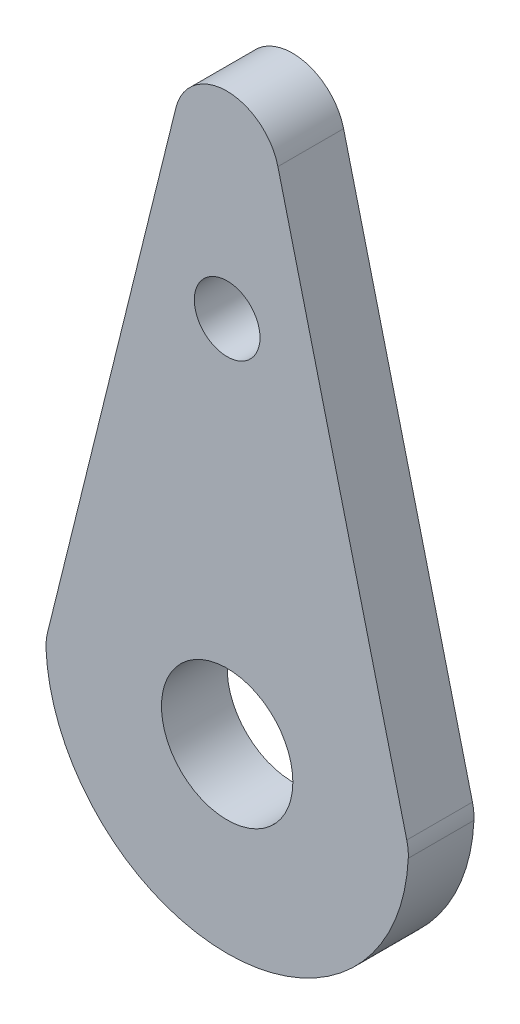
SolidWorks part; units mm, degrees
ref_plane "Front Plane" through (0, 0, 0) normal (0, 0, 1) x (1, 0, 0)
ref_plane "Top Plane" through (0, 0, 0) normal (0, 1, 0) x (1, 0, 0)
ref_plane "Right Plane" through (0, 0, 0) normal (1, 0, 0) x (0, 0, -1)
sketch "Sketch1" plane through (0, 0, 0) normal (0, 0, 1) x (1, 0, 0)
  line L0 (-8.6822, 0.3266) -> (-2.4777, 25.4)
  line L1 (2.453, 25.4022) -> (8.6816, 0.3278)
  circle A0 centre (0, 0) radius 3.175
  arc A1 (-8.7539, -0.3992) -> (8.7538, -0.4007) centre (0, 0) ccw
  arc A2 (2.453, 25.4022) -> (-2.4777, 25.4) centre (-0.0121, 24.7899) ccw
  circle A3 centre (0, 0) radius 8.763 construction
  arc A4 (-8.7539, -0.3992) -> (-8.6822, 0.3266) centre (-6.2165, -0.2835) cw
  arc A5 (8.7538, -0.4007) -> (8.6816, 0.3278) centre (6.2165, -0.2845) ccw
  point P12 (-8.763, 0)
  point P15 (8.763, 0)
  dimension "D1" = 6.35
  dimension "D3" = 2.54
  dimension "D6" = 2.54
  dimension "D7" = 2.54
  dimension "D4" = 25.4
  dimension "D5" = 25.4022
  dimension "D2" = 5.588
extrude "Boss-Extrude1" add sketch "Sketch1" along normal blind 3.175
hole_wizard "1/8 (0.125) Diameter Hole1" positions "Sketch3" profile "Sketch2" hole size "1/8" standard "ANSI Inch"
sketch "Sketch3" plane through (0, 0, 3.175) normal (0, 0, 1) x (1, 0, 0)
  arc A0 (2.453, 25.4022) -> (-2.4777, 25.4) centre (-0.0121, 24.7899) ccw construction
  point P0 (0, 17.8049)
  point P3 (-0.0132, 27.3299)
  dimension "D1" = 9.525
sketch "Sketch2" plane through (0, 17.8049, 3.175) normal (1, 0, 0) x (0, -1, 0)
  line L0 (0, 0) -> (0, 4.1279)
  line L1 (0, 4.1279) -> (1.5875, 3.174)
  line L2 (1.5875, 3.174) -> (1.5875, 0)
  line L5 (1.5875, 0) -> (0, 0)
  line L10 (0, 4.1279) -> (-1.5875, 3.174) construction
  line L11 (0, -6.35) -> (0, 107.95) construction
  dimension "Hole Dia." = 3.175
  dimension "Hole Depth" = 3.174
  dimension "Drill Angle" = 118
